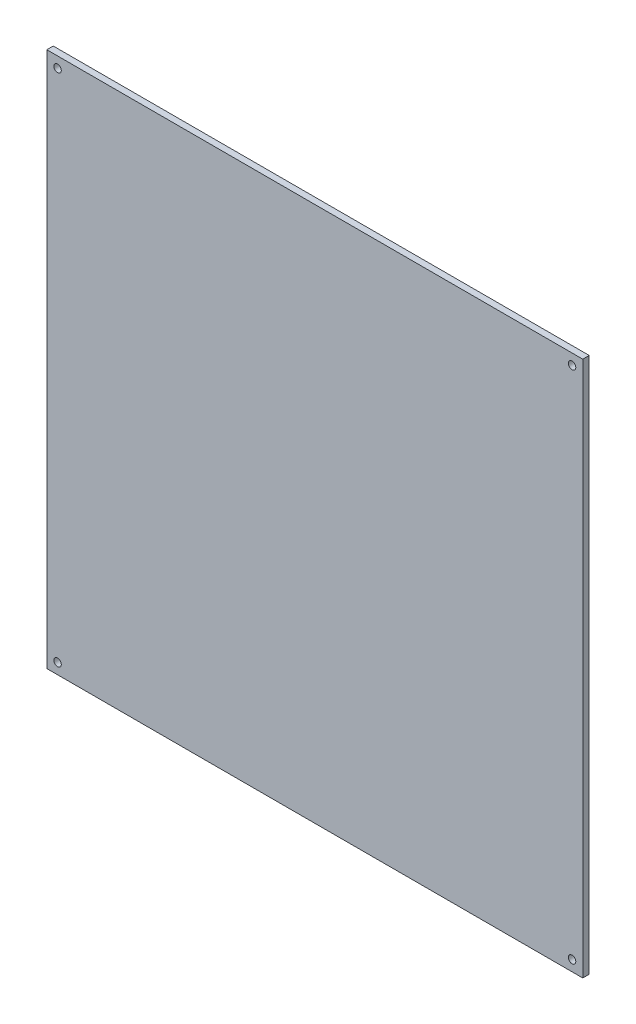
SolidWorks part; units mm, degrees
ref_plane "Front Plane" through (0, 0, 0) normal (0, 0, 1) x (1, 0, 0)
ref_plane "Top Plane" through (0, 0, 0) normal (0, 1, 0) x (1, 0, 0)
ref_plane "Right Plane" through (0, 0, 0) normal (1, 0, 0) x (0, 0, -1)
sketch "Sketch1" plane through (0, 0, 0) normal (0, 0, 1) x (1, 0, 0)
  line L1 (-125, 125) -> (125, 125)
  line L2 (-125, 125) -> (-125, -125)
  line L3 (-125, -125) -> (125, -125)
  line L4 (125, 125) -> (125, -125)
  line L5 (-125, 125) -> (125, -125) construction
  line L6 (-125, -125) -> (125, 125) construction
  point P0 (0, 0)
  dimension "D1" = 250
  dimension "D2" = 250
extrude "Boss-Extrude1" add sketch "Sketch1" along normal blind 3
sketch "Sketch3" plane through (0, 0, 3) normal (0, 0, 1) x (1, 0, 0)
  circle A0 centre (-120, 120) radius 1.75
  circle A1 centre (120, 120) radius 1.75
  circle A2 centre (-120, -120) radius 1.75
  circle A3 centre (120, -120) radius 1.75
extrude "Cut-Extrude1" cut sketch "Sketch3" against normal blind 3
